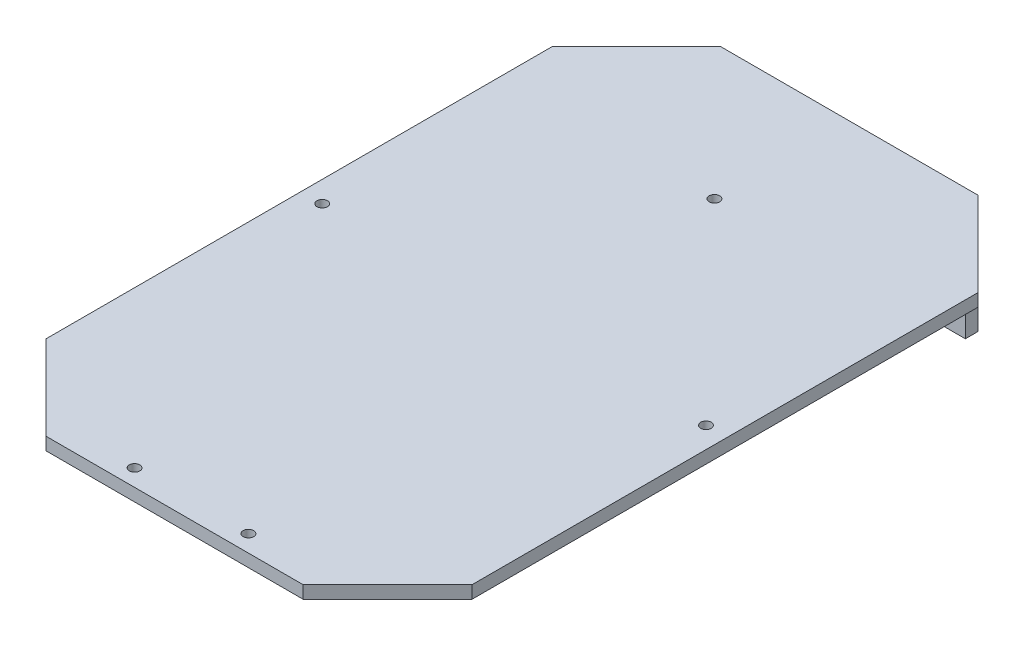
SolidWorks part; units mm, degrees
ref_plane "Plano frontal" through (0, 0, 0) normal (0, 0, 1) x (1, 0, 0)
ref_plane "Plano superior" through (0, 0, 0) normal (0, 1, 0) x (1, 0, 0)
ref_plane "Plano direito" through (0, 0, 0) normal (1, 0, 0) x (0, 0, -1)
sketch "Esboço1" plane through (0, 0, 0) normal (0, 1, 0) x (1, 0, 0)
  line L1 (-80.7703, 57.9537) -> (20.2297, 57.9537)
  line L2 (-80.7703, 57.9537) -> (-80.7703, -102.0463)
  line L3 (-80.7703, -102.0463) -> (20.2297, -102.0463)
  line L4 (20.2297, 57.9537) -> (20.2297, -102.0463)
  dimension "D1" = 160
  dimension "D2" = 101
extrude "Ressalto-extrusão1" add sketch "Esboço1" along normal blind 3
sketch "Esboço2" plane through (0, 3, 0) normal (0, 1, 0) x (1, 0, 0)
  line L0 (20.2297, -102.0463) -> (20.2297, 57.9537) construction
  circle A0 centre (15.2297, -21.5463) radius 1.25
  circle A1 centre (-75.7703, -21.5463) radius 1.25
  circle A2 centre (-30.2703, 25.9537) radius 1.25
  circle A3 centre (-43.7703, -98.0463) radius 1.25
  circle A4 centre (-16.7703, -98.0463) radius 1.25
  point P2 (20.2297, -22.0463)
  point P19 (-30.2703, -96.8916)
extrude "Corte-extrusão1" cut sketch "Esboço2" against normal blind 140
chamfer "Chanfro1" distance 20 angle 45 4 edges at (-80.7703, 1.5, 102.0463) (20.2297, 1.5, 102.0463) (20.2297, 1.5, -57.9537) (-80.7703, 1.5, -57.9537)
sketch "Esboço3" plane through (0, 0, 0) normal (0, -1, 0) x (1, 0, 0)
  line L1 (0.2297, -57.9537) -> (-60.7703, -57.9537)
  line L2 (0.2297, -57.9537) -> (0.2297, -54.9537)
  line L3 (0.2297, -54.9537) -> (-60.7703, -54.9537)
  line L4 (-60.7703, -57.9537) -> (-60.7703, -54.9537)
  dimension "D1" = 3
extrude "Ressalto-extrusão2" add sketch "Esboço3" along normal blind 25
sketch "Esboço4" plane through (0, 0, -57.9537) normal (0, 0, -1) x (-1, 0, 0)
  line L0 (-0.2297, -25) -> (-0.2297, 0) construction
  line L1 (60.7703, -25) -> (-0.2297, -25) construction
  circle A0 centre (9.7703, -5.5) radius 0.5
  circle A1 centre (50.7703, -21) radius 0.5
  circle A2 centre (9.7703, -21) radius 0.5
  circle A3 centre (50.7703, -5.5) radius 0.5
  dimension "D1" = 1
  dimension "D2" = 0
  dimension "D4" = 10
  dimension "D3" = 15.5
  dimension "D5" = 4
  dimension "D6" = 4
  dimension "D7" = 15.5
extrude "Corte-extrusão2" cut sketch "Esboço4" against normal blind 25
